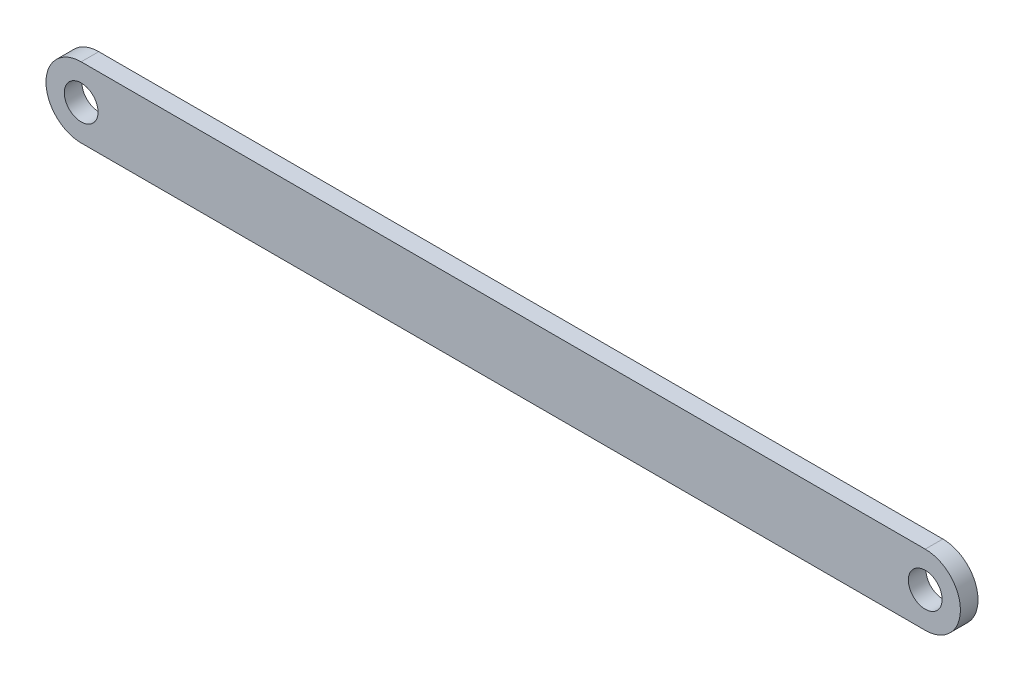
SolidWorks part; units mm, degrees
ref_plane "Front Plane" through (0, 0, 0) normal (0, 0, 1) x (1, 0, 0)
ref_plane "Top Plane" through (0, 0, 0) normal (0, 1, 0) x (1, 0, 0)
ref_plane "Right Plane" through (0, 0, 0) normal (1, 0, 0) x (0, 0, -1)
sketch "Sketch1" plane through (0, 0, 0) normal (0, 0, 1) x (1, 0, 0)
  line L1 (-76.2, -6.35) -> (76.2, -6.35)
  line L2 (-76.2, -6.35) -> (-76.2, 6.35) construction
  line L3 (-76.2, 6.35) -> (76.2, 6.35)
  line L4 (76.2, -6.35) -> (76.2, 6.35) construction
  line L5 (-76.2, -6.35) -> (76.2, 6.35) construction
  line L6 (-76.2, 6.35) -> (76.2, -6.35) construction
  arc A0 (76.2, 6.35) -> (76.2, -6.35) centre (76.2, 0) cw
  arc A1 (-76.2, 6.35) -> (-76.2, -6.35) centre (-76.2, 0) ccw
  circle A2 centre (-76.2, 0) radius 3.048
  circle A3 centre (76.2, 0) radius 3.048
  point P0 (0, 0)
  dimension "D3" = 6.096
  dimension "D4" = 6.096
  dimension "D1" = 152.4
  dimension "D2" = 12.7
extrude "Boss-Extrude1" add sketch "Sketch1" along normal blind 3.175
